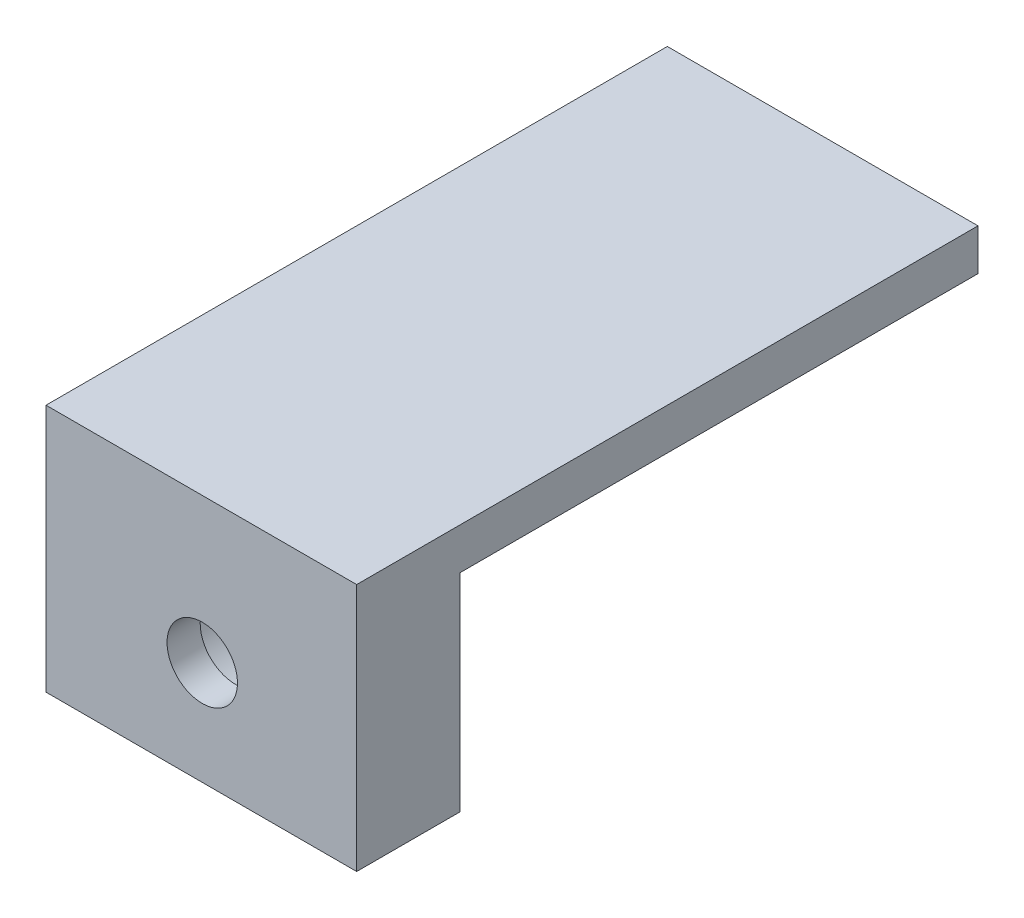
SolidWorks part; units mm, degrees
ref_plane "前视基准面" through (0, 0, 0) normal (0, 0, 1) x (1, 0, 0)
ref_plane "上视基准面" through (0, 0, 0) normal (0, 1, 0) x (1, 0, 0)
ref_plane "右视基准面" through (0, 0, 0) normal (1, 0, 0) x (0, 0, -1)
sketch "草图1" plane through (0, 0, 0) normal (0, 0, 1) x (1, 0, 0)
  line L1 (0, 0) -> (15, 0)
  line L2 (0, 0) -> (0, 12)
  line L3 (0, 12) -> (15, 12)
  line L4 (15, 0) -> (15, 12)
  dimension "D1" = 15
  dimension "D2" = 12
extrude "凸台-拉伸1" add sketch "草图1" along normal blind 5
sketch "草图2" plane through (0, 0, 0) normal (0, 0, -1) x (-1, 0, 0)
  line L0 (0, 6) -> (-15, 6) construction
  line L1 (0, 12) -> (0, 0) construction
  line L2 (-15, 0) -> (-15, 12) construction
  line L4 (0, 5) -> (-15, 5)
  line L5 (0, 5) -> (0, 7)
  line L6 (0, 7) -> (-15, 7)
  line L7 (-15, 5) -> (-15, 7)
  dimension "D1" = 2
extrude "凸台-拉伸2" add sketch "草图2" along normal blind 25
sketch "草图6" plane through (0, 0, 0) normal (0, 0, -1) x (-1, 0, 0)
  line L1 (0, 12) -> (-15, 12)
  line L2 (0, 12) -> (0, 7)
  line L3 (0, 7) -> (-15, 7)
  line L4 (-15, 12) -> (-15, 7)
extrude "切除-拉伸2" cut sketch "草图6" against normal through all
sketch "草图7" plane through (0, 0, 0) normal (0, -1, 0) x (1, 0, 0)
  line L1 (15, 5) -> (0, 5)
  line L2 (15, 5) -> (15, 0)
  line L3 (15, 0) -> (0, 0)
  line L4 (0, 5) -> (0, 0)
extrude "凸台-拉伸3" add sketch "草图7" along normal blind 5
hole_wizard "M3 六角凹头螺钉的柱形沉头孔1" positions "草图8" profile "草图9" counterbore size "M3" standard "ISO"
sketch "草图8" plane through (0, 0, 0) normal (0, 0, -1) x (-1, 0, 0)
  line L0 (-7.5, -5) -> (-7.5, 5) construction
  line L1 (0, -5) -> (-15, -5) construction
  line L2 (-15, 5) -> (0, 5) construction
  line L3 (-7.5, 5) -> (-7.5, 0) construction
  line L4 (-7.5, 0) -> (-15.899, 0) construction
  point P0 (-7.5443, 0)
  point P14 (0, 0)
sketch "草图9" plane through (7.5443, 0, 0) normal (1, 0, 0) x (0, 1, 0)
  line L0 (0, 0) -> (0, 8.5215)
  line L1 (0, 8.5215) -> (1.7, 7.5)
  line L2 (1.7, 7.5) -> (1.7, 3.4)
  line L3 (1.7, 3.4) -> (3.25, 3.4)
  line L4 (3.25, 3.4) -> (3.25, 0)
  line L5 (3.25, 0) -> (0, 0)
  line L10 (0, 8.5215) -> (-1.7, 7.5) construction
  line L11 (0, -6.35) -> (0, 107.95) construction
  dimension "孔直径" = 3.4
  dimension "孔深度" = 7.5
  dimension "柱形沉头孔直径" = 6.5
  dimension "柱形沉头孔深度" = 3.4
  dimension "导头角度" = 118
